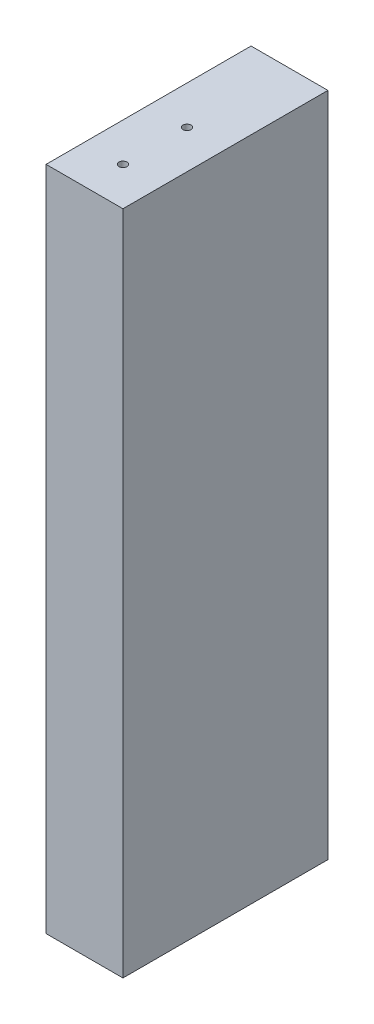
SolidWorks part; units mm, degrees
material "MDF"
ref_plane "Front" through (0, 0, 0) normal (0, 0, 1) x (1, 0, 0)
ref_plane "Top" through (0, 0, 0) normal (0, 1, 0) x (1, 0, 0)
ref_plane "Right" through (0, 0, 0) normal (1, 0, 0) x (0, 0, -1)
sketch "Sketch1" plane through (0, 0, 0) normal (0, 0, 1) x (1, 0, 0)
  line L0 (273.05, 6101.08) -> (475.4926, 6101.08) construction
  line L1 (450.0926, 6101.08) -> (431.0426, 6101.08)
  line L2 (450.0926, 6101.08) -> (450.0926, 6266.18)
  line L3 (450.0926, 6266.18) -> (431.0426, 6266.18)
  line L4 (431.0426, 6101.08) -> (431.0426, 6266.18)
  line L5 (481.7563, 6266.18) -> (273.05, 6266.18) construction
  dimension "D1" = 25.4
  dimension "D2" = 19.05
extrude "Boss-Extrude1" add sketch "Sketch1" along normal blind 50.8
hole_wizard "5/64 (0.07813) Diameter Hole1" positions "Sketch2" profile "Sketch3" hole size "5/64" standard "ANSI Inch"
sketch "Sketch2" plane through (4.969, 0, -19.0501) normal (0, 0, -1) x (-1, 0, 0)
  point P0 (-481.5892, 6993.255)
  point P9 (-386.3392, 6993.255)
  point P18 (-291.0892, 6993.255)
  point P21 (-295.275, 6965.1359)
  point P33 (-295.275, 6812.7359)
  point P45 (-295.275, 6660.3359)
  point P48 (-285.1664, 6631.4688)
  point P66 (-475.4773, 6631.4688)
  point P69 (-485.0023, 6660.3359)
  point P81 (-485.0023, 6812.7359)
  point P93 (-485.0023, 6965.1359)
  point P96 (-478.3656, 6611.6708)
  point P114 (-287.8656, 6611.6708)
  point P117 (-307.975, 6564.3379)
  point P127 (-307.975, 6488.1379)
  point P130 (-284.9609, 6440.805)
  point P143 (-380.2109, 6440.805)
  point P152 (-475.4609, 6440.805)
  point P155 (-446.8313, 6488.1379)
  point P161 (-446.8313, 6564.3379)
  point P164 (-472.2313, 6396.355)
  point P170 (-472.2313, 6320.155)
  point P173 (-472.6532, 6275.705)
  point P182 (-377.4032, 6275.705)
  point P191 (-282.1532, 6275.705)
  point P194 (-282.575, 6320.155)
  point P200 (-282.575, 6396.355)
  point P203 (-435.5986, 6221.73)
  point P209 (-435.5986, 6145.53)
  point P233 (-450.5925, 6091.555)
  point P242 (-460.9986, 6091.5555)
  point P245 (-460.9986, 6056.63)
  point P251 (-460.9986, 5980.43)
  point P263 (-460.9986, 5945.505)
  point P280 (-282.1532, 5945.505)
  point P284 (-368.6118, 5945.505)
sketch "Sketch3" plane through (486.5582, 6993.255, -19.0501) normal (1, 0, 0) x (0, 1, 0)
  line L0 (0, 0) -> (0, 38.6962)
  line L1 (0, 38.6962) -> (0.9923, 38.1)
  line L2 (0.9923, 38.1) -> (0.9923, 0)
  line L3 (0.9923, 0) -> (0, 0)
  line L4 (0, 38.6962) -> (-0.9923, 38.1) construction
  line L5 (0, -6.35) -> (0, 107.95) construction
  dimension "Hole Dia." = 1.9845
  dimension "Hole Depth" = 38.1
  dimension "Drill Angle" = 118
hole_wizard "5/64 (0.07813) Diameter Hole2" positions "Sketch4" profile "Sketch5" hole size "5/64" standard "ANSI Inch"
sketch "Sketch4" plane through (0, 6101.08, 0) normal (0, -1, 0) x (-1, 0, 0)
  line L0 (-440.5676, -50.8) -> (-440.5676, 0.0001) construction
  line L1 (-431.0426, -50.8) -> (-450.0926, -50.8) construction
  line L2 (-480.4616, 0) -> (-430.6614, 0.0001) construction
  point P0 (-440.5676, -41.275)
  point P2 (-440.5676, -25.4)
  dimension "D1" = 15.875
sketch "Sketch5" plane through (440.5676, 6101.08, 41.275) normal (1, 0, 0) x (0, 0, -1)
  line L0 (0, 0) -> (0, 19.6462)
  line L1 (0, 19.6462) -> (0.9923, 19.05)
  line L2 (0.9923, 19.05) -> (0.9923, 0)
  line L5 (0.9923, 0) -> (0, 0)
  line L10 (0, 19.6462) -> (-0.9923, 19.05) construction
  line L11 (0, -6.35) -> (0, 107.95) construction
  dimension "Hole Dia." = 1.9845
  dimension "Hole Depth" = 19.05
  dimension "Drill Angle" = 118
hole_wizard "5/64 (0.07813) Diameter Hole3" positions "Sketch6" profile "Sketch7" hole size "5/64" standard "ANSI Inch"
sketch "Sketch6" plane through (0, 6266.18, 0) normal (0, 1, 0) x (1, 0, 0)
  circle A0 centre (440.5676, -41.275) radius 0.9923 construction
  circle A1 centre (440.5676, -25.4) radius 0.9923 construction
  point P0 (440.5676, -25.4)
  point P2 (440.5676, -41.275)
sketch "Sketch7" plane through (440.5676, 6266.18, 25.4) normal (1, 0, 0) x (0, 0, 1)
  line L0 (0, 0) -> (0, 19.6462)
  line L1 (0, 19.6462) -> (0.9923, 19.05)
  line L2 (0.9923, 19.05) -> (0.9923, 0)
  line L5 (0.9923, 0) -> (0, 0)
  line L10 (0, 19.6462) -> (-0.9923, 19.05) construction
  line L11 (0, -6.35) -> (0, 107.95) construction
  dimension "Hole Dia." = 1.9845
  dimension "Hole Depth" = 19.05
  dimension "Drill Angle" = 118
